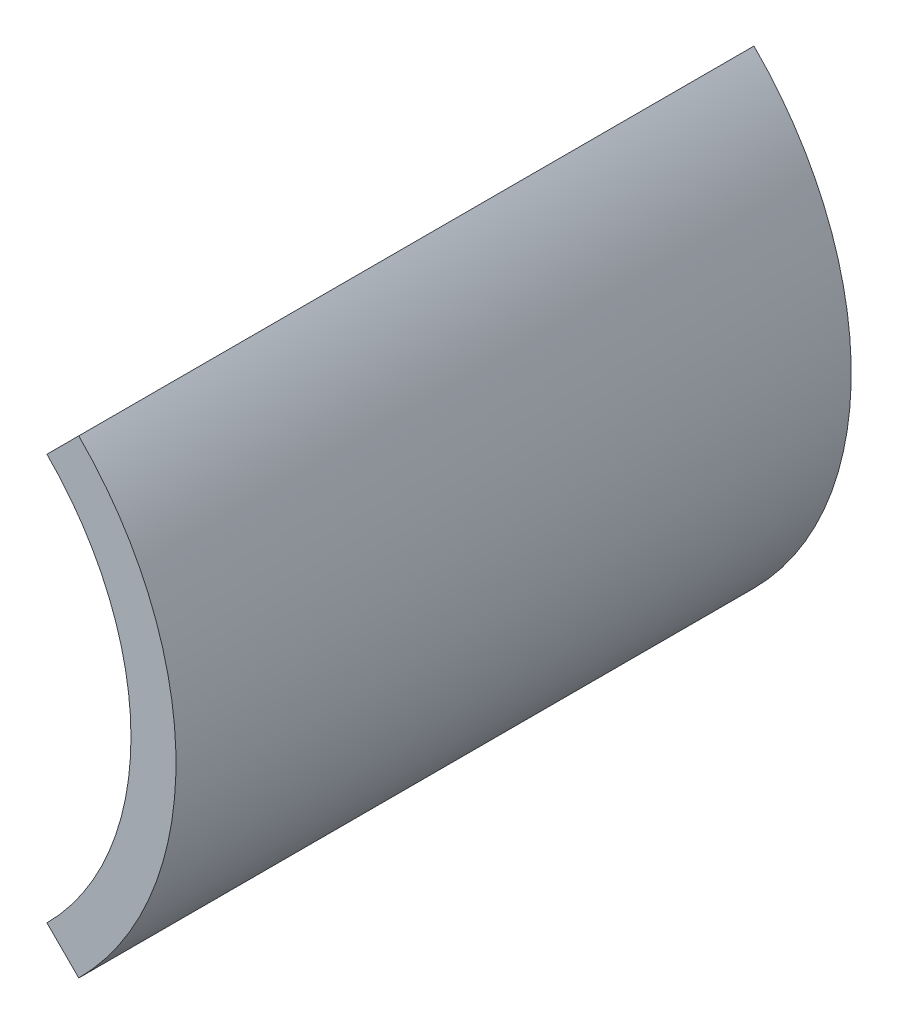
SolidWorks part; units mm, degrees
ref_plane "Front Plane" through (0, 0, 0) normal (0, 0, 1) x (1, 0, 0)
ref_plane "Top Plane" through (0, 0, 0) normal (0, 1, 0) x (1, 0, 0)
ref_plane "Right Plane" through (0, 0, 0) normal (1, 0, 0) x (0, 0, -1)
sketch "Sketch1" plane through (0, 0, 0) normal (0, 0, 1) x (1, 0, 0)
  line L0 (0, 0) -> (19.2185, 0) construction
  line L1 (9.0156, 9.0156) -> (10.4298, 10.4298)
  line L2 (9.0156, -9.0156) -> (10.4298, -10.4298)
  arc A0 (9.0156, -9.0156) -> (9.0156, 9.0156) centre (0, 0) ccw
  arc A1 (10.4298, -10.4298) -> (10.4298, 10.4298) centre (0, 0) ccw
  dimension "D1" = 29.5
  dimension "D2" = 25.5
  dimension "D3" = 90
extrude "Boss-Extrude1" add sketch "Sketch1" along normal mid plane 30
